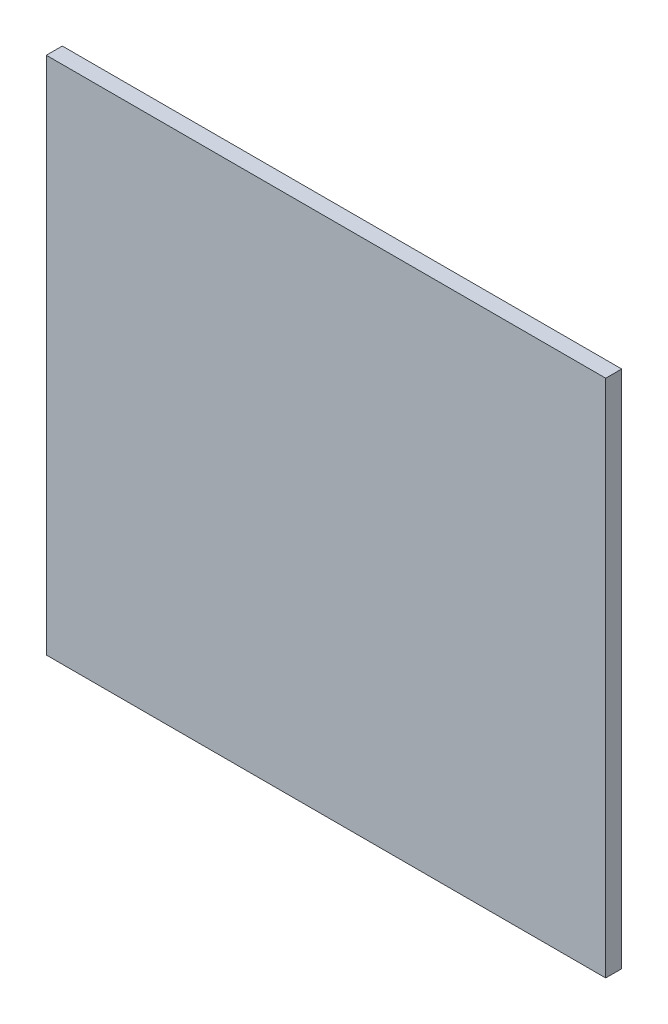
SolidWorks part; units mm, degrees
material "Maple"
ref_plane "Front Plane" through (0, 0, 0) normal (0, 0, 1) x (1, 0, 0)
ref_plane "Top Plane" through (0, 0, 0) normal (0, 1, 0) x (1, 0, 0)
ref_plane "Right Plane" through (0, 0, 0) normal (1, 0, 0) x (0, 0, -1)
sketch "Sketch1" plane through (0, 0, 0) normal (0, 0, 1) x (1, 0, 0)
  line L1 (-70, -65) -> (70, -65)
  line L2 (-70, -65) -> (-70, 65)
  line L3 (-70, 65) -> (70, 65)
  line L4 (70, -65) -> (70, 65)
  line L5 (-70, -65) -> (70, 65) construction
  line L6 (-70, 65) -> (70, -65) construction
  point P0 (0, 0)
  dimension "D1" = 130
  dimension "D2" = 140
extrude "Boss-Extrude1" add sketch "Sketch1" along normal blind 4
